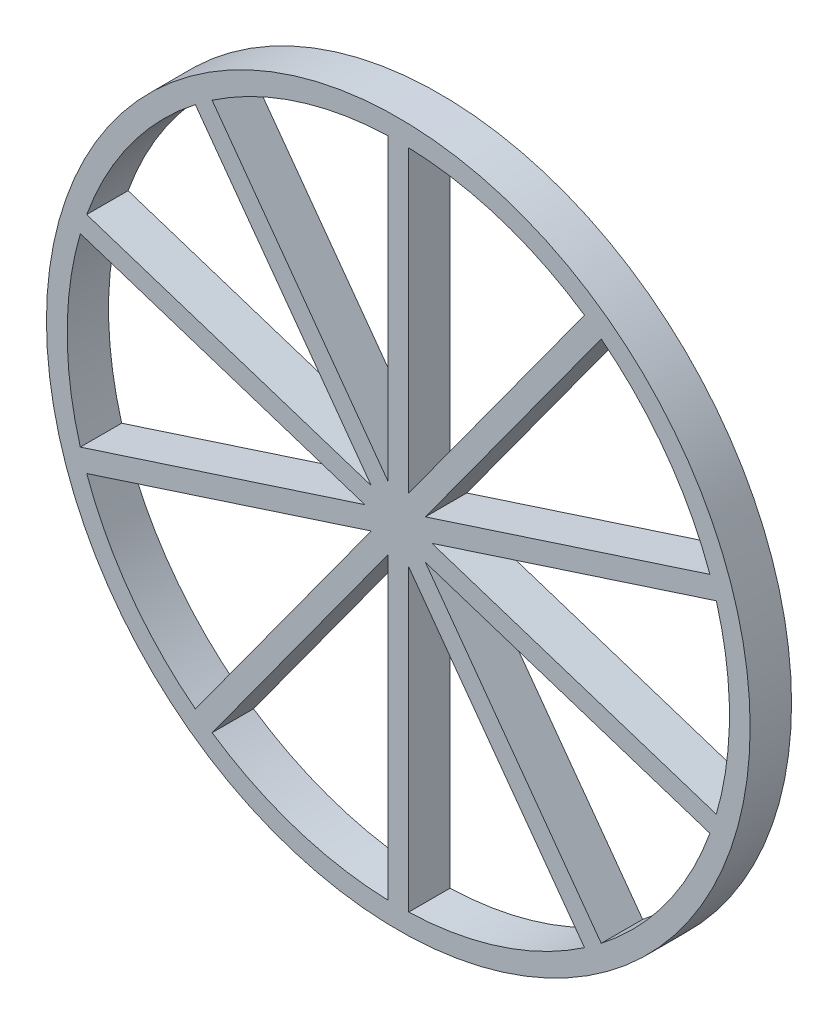
SolidWorks part; units mm, degrees
ref_plane "Plano frontal" through (0, 0, 0) normal (0, 0, 1) x (1, 0, 0)
ref_plane "Plano superior" through (0, 0, 0) normal (0, 1, 0) x (1, 0, 0)
ref_plane "Plano direito" through (0, 0, 0) normal (1, 0, 0) x (0, 0, -1)
sketch "Esboço1" plane through (0, 0, 0) normal (0, 0, 1) x (1, 0, 0)
  line L23 (-0.6545, 0.4755) -> (-4.9022, 6.322)
  line L24 (-0.6545, 0.4755) -> (-7.5275, 2.7087)
  line L25 (-0.25, 0.7694) -> (-0.25, 7.9961)
  line L26 (0.25, 0.7694) -> (4.4977, 6.6159)
  line L29 (-0.25, 0.7694) -> (-4.4977, 6.6159)
  line L30 (0.25, 0.7694) -> (0.25, 7.9961)
  line L31 (0.6545, 0.4755) -> (7.5275, 2.7087)
  line L32 (0.6545, 0.4755) -> (4.9022, 6.322)
  line L33 (0.809, 0) -> (7.682, -2.2332)
  line L34 (0.809, 0) -> (7.682, 2.2332)
  line L35 (0.6545, -0.4755) -> (4.9022, -6.322)
  line L36 (0.25, -0.7694) -> (0.25, -7.9961)
  line L37 (0.6545, -0.4755) -> (7.5275, -2.7087)
  line L38 (-0.25, -0.7694) -> (-4.4977, -6.6159)
  line L39 (0.25, -0.7694) -> (4.4977, -6.6159)
  line L40 (-0.25, -0.7694) -> (-0.25, -7.9961)
  line L41 (-0.6545, -0.4755) -> (-7.5275, -2.7087)
  line L42 (-0.6545, -0.4755) -> (-4.9022, -6.322)
  line L43 (-0.809, 0) -> (-7.682, 2.2332)
  line L44 (-0.809, 0) -> (-7.682, -2.2332)
  circle A0 centre (0, 0) radius 8.5
  arc A1 (-0.25, 7.9961) -> (-4.4977, 6.6159) centre (0, 0) ccw
  arc A2 (-4.9022, 6.322) -> (-7.5275, 2.7087) centre (0, 0) ccw
  arc A3 (4.4977, 6.6159) -> (0.25, 7.9961) centre (0, 0) ccw
  arc A4 (7.5275, 2.7087) -> (4.9022, 6.322) centre (0, 0) ccw
  arc A5 (7.682, -2.2332) -> (7.682, 2.2332) centre (0, 0) ccw
  arc A6 (0.25, -7.9961) -> (4.4977, -6.6159) centre (0, 0) ccw
  arc A7 (4.9022, -6.322) -> (7.5275, -2.7087) centre (0, 0) ccw
  arc A8 (-4.4977, -6.6159) -> (-0.25, -7.9961) centre (0, 0) ccw
  arc A9 (-7.5275, -2.7087) -> (-4.9022, -6.322) centre (0, 0) ccw
  arc A10 (-7.682, 2.2332) -> (-7.682, -2.2332) centre (0, 0) ccw
  point P50 (0, 0)
  dimension "D1" = 0.5
  dimension "D2" = 17
extrude "Ressalto-extrusão1" add sketch "Esboço1" along normal blind 1
